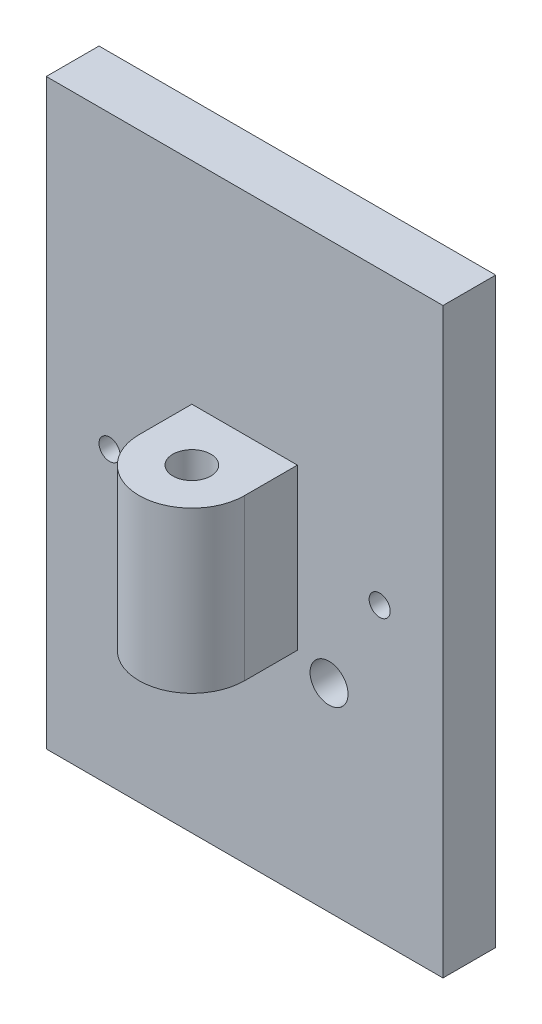
SolidWorks part; units mm, degrees
ref_plane "Front Plane" through (0, 0, 0) normal (0, 0, 1) x (1, 0, 0)
ref_plane "Top Plane" through (0, 0, 0) normal (0, 1, 0) x (1, 0, 0)
ref_plane "Right Plane" through (0, 0, 0) normal (1, 0, 0) x (0, 0, -1)
sketch "Sketch1" plane through (0, 0, 0) normal (0, 0, 1) x (1, 0, 0)
  line L1 (0, 0) -> (23.876, 0)
  line L2 (0, 0) -> (0, 35.052)
  line L3 (0, 35.052) -> (23.876, 35.052)
  line L4 (23.876, 0) -> (23.876, 35.052)
  circle A0 centre (6.858, 11.938) radius 1.143
  circle A1 centre (17.018, 11.938) radius 1.143
  circle A2 centre (20.066, 17.526) radius 0.635
  circle A3 centre (3.81, 17.526) radius 0.635
  dimension "D5" = 2.286
  dimension "D7" = 2.286
  dimension "D9" = 1.27
  dimension "D12" = 1.27
  dimension "D1" = 23.876
  dimension "D2" = 35.052
  dimension "D3" = 6.858
  dimension "D4" = 10.16
  dimension "D6" = 11.938
  dimension "D8" = 11.938
  dimension "D10" = 3.81
  dimension "D11" = 17.526
  dimension "D13" = 3.81
  dimension "D14" = 17.526
extrude "Boss-Extrude1" add sketch "Sketch1" along normal blind 3.175
sketch "Sketch2" plane through (0, 0, 0) normal (0, 0, 1) x (1, 0, 0)
  line L0 (23.876, 35.052) -> (0, 35.052) construction
  line L1 (8.763, 12.7) -> (15.113, 12.7)
  line L2 (8.763, 12.7) -> (8.763, 22.352)
  line L3 (8.763, 22.352) -> (15.113, 22.352)
  line L4 (15.113, 12.7) -> (15.113, 22.352)
  line L5 (0, 0) -> (23.876, 0) construction
  line L6 (0, 35.052) -> (0, 0) construction
  dimension "D1" = 6.35
  dimension "D2" = 12.7
  dimension "D3" = 12.7
  dimension "D4" = 8.763
extrude "Boss-Extrude2" add sketch "Sketch2" along normal blind 9.525
sketch "Sketch3" plane through (0, 0, 0) normal (0, 1, 0) x (1, 0, 0)
  line L0 (15.113, -9.525) -> (8.763, -9.525) construction
  line L1 (8.763, -9.525) -> (8.763, -3.175) construction
  line L2 (15.113, -9.525) -> (15.113, -3.175) construction
  line L3 (8.763, -6.35) -> (8.763, -9.525)
  line L4 (8.763, -9.525) -> (15.113, -9.525)
  line L5 (15.113, -9.525) -> (15.113, -6.35)
  circle A0 centre (11.938, -6.35) radius 1.143
  arc A1 (8.763, -6.35) -> (15.113, -6.35) centre (11.938, -6.35) ccw
  point P4 (11.938, -9.525)
  dimension "D1" = 2.286
  dimension "D2" = 3.175
  dimension "D3" = 3.175
extrude "Cut-Extrude2" cut sketch "Sketch3" against normal blind 6.35 and the other way through all contours A0 | A1 L3 L4 | A1 L4 L5
